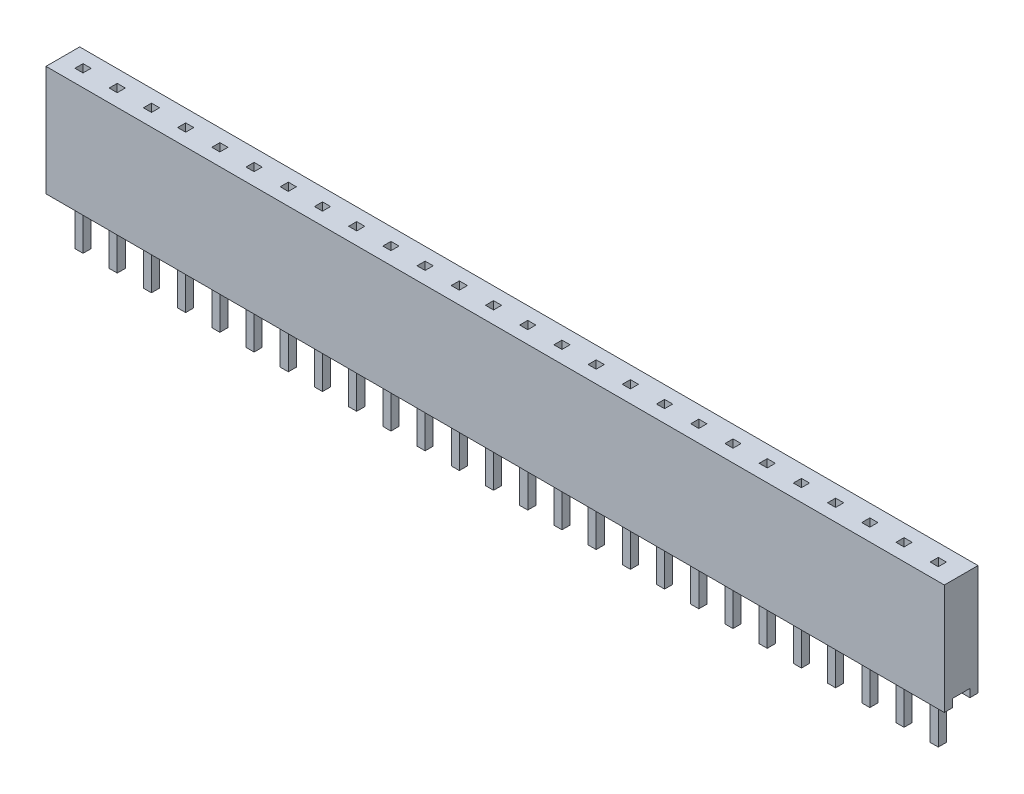
SolidWorks part; units mm, degrees
ref_plane "Front" through (0, 0, 0) normal (0, 0, 1) x (1, 0, 0)
ref_plane "Top" through (0, 0, 0) normal (0, 1, 0) x (1, 0, 0)
ref_plane "Right" through (0, 0, 0) normal (1, 0, 0) x (0, 0, -1)
sketch "Sketch1" plane through (0, 0, 0) normal (0, 1, 0) x (1, 0, 0)
  line L1 (0, 0) -> (66.7004, 0)
  line L2 (0, 0) -> (0, 2.5)
  line L3 (0, 2.5) -> (66.7004, 2.5)
  line L4 (66.7004, 0) -> (66.7004, 2.5)
  dimension "D1" = 66.7004
  dimension "D2" = 2.5
extrude "Body" add sketch "Sketch1" against normal blind 8.2
sketch "Sketch2" plane through (66.7004, 0, 0) normal (1, 0, 0) x (0, 0, -1)
  line L0 (1.25, 0) -> (1.25, -8.2) construction
  line L1 (0, 0) -> (2.5, 0) construction
  line L2 (0, -8.2) -> (2.5, -8.2) construction
  line L3 (0, -8.2) -> (0, 0) construction
  line L4 (0.6, -8.2) -> (1.9, -8.2)
  line L5 (0.6, -8.2) -> (0.6, -7.6)
  line L6 (0.6, -7.6) -> (1.9, -7.6)
  line L7 (1.9, -8.2) -> (1.9, -7.6)
  line L8 (0.6, -8.2) -> (1.9, -7.6) construction
  line L9 (0.6, -7.6) -> (1.9, -8.2) construction
  point P6 (1.25, -7.9)
  dimension "D1" = 0.6
  dimension "D2" = 0.6
extrude "Base Cut" cut sketch "Sketch2" against normal through all
sketch "Sketch3" plane through (0, 0, 0) normal (0, 1, 0) x (1, 0, 0)
  line L0 (0, 1.25) -> (5.2601, 1.25) construction
  line L1 (0, 2.5) -> (0, 0) construction
  line L5 (1.2, 1.55) -> (1.8, 0.95) construction
  line L13 (1.2, 0.95) -> (1.8, 1.55) construction
  line L14 (1.8, 1.55) -> (1.8, 0.95)
  line L15 (1.2, 1.55) -> (1.8, 1.55)
  line L16 (1.2, 1.55) -> (1.2, 0.95)
  line L17 (1.2, 0.95) -> (1.8, 0.95)
  point P11 (1.5, 1.25)
  dimension "D1" = 0.6
  dimension "D2" = 0.6
  dimension "D3" = 1.5
extrude "Pin Hole" cut sketch "Sketch3" against normal through all
pattern_linear "LPattern1" count 26 spacing 2.54 along (1, 0, 0) of "Pin Hole"
sketch "Sketch5" plane through (0, -7.6, 0) normal (0, -1, 0) x (1, 0, 0)
  line L0 (1.8, -0.95) -> (1.8, -1.55) construction
  line L1 (1.8, -1.55) -> (1.2, -1.55) construction
  line L2 (1.2, -1.55) -> (1.2, -0.95) construction
  line L3 (1.2, -0.95) -> (1.8, -0.95) construction
  line L4 (1.8, -0.95) -> (1.8, -1.55)
  line L5 (1.8, -1.55) -> (1.2, -1.55)
  line L6 (1.2, -1.55) -> (1.2, -0.95)
  line L7 (1.2, -0.95) -> (1.8, -0.95)
  line L16 (4.34, -0.95) -> (4.34, -1.55)
  line L17 (4.34, -1.55) -> (3.74, -1.55)
  line L18 (3.74, -1.55) -> (3.74, -0.95)
  line L19 (3.74, -0.95) -> (4.34, -0.95)
  line L24 (6.88, -0.95) -> (6.88, -1.55)
  line L25 (6.88, -1.55) -> (6.28, -1.55)
  line L26 (6.28, -1.55) -> (6.28, -0.95)
  line L27 (6.28, -0.95) -> (6.88, -0.95)
  line L32 (9.42, -0.95) -> (9.42, -1.55)
  line L33 (9.42, -1.55) -> (8.82, -1.55)
  line L34 (8.82, -1.55) -> (8.82, -0.95)
  line L35 (8.82, -0.95) -> (9.42, -0.95)
  line L40 (11.96, -0.95) -> (11.96, -1.55)
  line L41 (11.96, -1.55) -> (11.36, -1.55)
  line L42 (11.36, -1.55) -> (11.36, -0.95)
  line L43 (11.36, -0.95) -> (11.96, -0.95)
  line L48 (14.5, -0.95) -> (14.5, -1.55)
  line L49 (14.5, -1.55) -> (13.9, -1.55)
  line L50 (13.9, -1.55) -> (13.9, -0.95)
  line L51 (13.9, -0.95) -> (14.5, -0.95)
  line L56 (17.04, -0.95) -> (17.04, -1.55)
  line L57 (17.04, -1.55) -> (16.44, -1.55)
  line L58 (16.44, -1.55) -> (16.44, -0.95)
  line L59 (16.44, -0.95) -> (17.04, -0.95)
  line L64 (19.58, -0.95) -> (19.58, -1.55)
  line L65 (19.58, -1.55) -> (18.98, -1.55)
  line L66 (18.98, -1.55) -> (18.98, -0.95)
  line L67 (18.98, -0.95) -> (19.58, -0.95)
  line L72 (22.12, -0.95) -> (22.12, -1.55)
  line L73 (22.12, -1.55) -> (21.52, -1.55)
  line L74 (21.52, -1.55) -> (21.52, -0.95)
  line L75 (21.52, -0.95) -> (22.12, -0.95)
  line L80 (24.66, -0.95) -> (24.66, -1.55)
  line L81 (24.66, -1.55) -> (24.06, -1.55)
  line L82 (24.06, -1.55) -> (24.06, -0.95)
  line L83 (24.06, -0.95) -> (24.66, -0.95)
  line L88 (27.2, -0.95) -> (27.2, -1.55)
  line L89 (27.2, -1.55) -> (26.6, -1.55)
  line L90 (26.6, -1.55) -> (26.6, -0.95)
  line L91 (26.6, -0.95) -> (27.2, -0.95)
  line L96 (29.74, -0.95) -> (29.74, -1.55)
  line L97 (29.74, -1.55) -> (29.14, -1.55)
  line L98 (29.14, -1.55) -> (29.14, -0.95)
  line L99 (29.14, -0.95) -> (29.74, -0.95)
  line L104 (32.28, -0.95) -> (32.28, -1.55)
  line L105 (32.28, -1.55) -> (31.68, -1.55)
  line L106 (31.68, -1.55) -> (31.68, -0.95)
  line L107 (31.68, -0.95) -> (32.28, -0.95)
  line L112 (34.82, -0.95) -> (34.82, -1.55)
  line L113 (34.82, -1.55) -> (34.22, -1.55)
  line L114 (34.22, -1.55) -> (34.22, -0.95)
  line L115 (34.22, -0.95) -> (34.82, -0.95)
  line L120 (37.36, -0.95) -> (37.36, -1.55)
  line L121 (37.36, -1.55) -> (36.76, -1.55)
  line L122 (36.76, -1.55) -> (36.76, -0.95)
  line L123 (36.76, -0.95) -> (37.36, -0.95)
  line L128 (39.9, -0.95) -> (39.9, -1.55)
  line L129 (39.9, -1.55) -> (39.3, -1.55)
  line L130 (39.3, -1.55) -> (39.3, -0.95)
  line L131 (39.3, -0.95) -> (39.9, -0.95)
  line L136 (42.44, -0.95) -> (42.44, -1.55)
  line L137 (42.44, -1.55) -> (41.84, -1.55)
  line L138 (41.84, -1.55) -> (41.84, -0.95)
  line L139 (41.84, -0.95) -> (42.44, -0.95)
  line L144 (44.98, -0.95) -> (44.98, -1.55)
  line L145 (44.98, -1.55) -> (44.38, -1.55)
  line L146 (44.38, -1.55) -> (44.38, -0.95)
  line L147 (44.38, -0.95) -> (44.98, -0.95)
  line L152 (47.52, -0.95) -> (47.52, -1.55)
  line L153 (47.52, -1.55) -> (46.92, -1.55)
  line L154 (46.92, -1.55) -> (46.92, -0.95)
  line L155 (46.92, -0.95) -> (47.52, -0.95)
  line L160 (50.06, -0.95) -> (50.06, -1.55)
  line L161 (50.06, -1.55) -> (49.46, -1.55)
  line L162 (49.46, -1.55) -> (49.46, -0.95)
  line L163 (49.46, -0.95) -> (50.06, -0.95)
  line L168 (52.6, -0.95) -> (52.6, -1.55)
  line L169 (52.6, -1.55) -> (52, -1.55)
  line L170 (52, -1.55) -> (52, -0.95)
  line L171 (52, -0.95) -> (52.6, -0.95)
  line L176 (55.14, -0.95) -> (55.14, -1.55)
  line L177 (55.14, -1.55) -> (54.54, -1.55)
  line L178 (54.54, -1.55) -> (54.54, -0.95)
  line L179 (54.54, -0.95) -> (55.14, -0.95)
  line L184 (57.68, -0.95) -> (57.68, -1.55)
  line L185 (57.68, -1.55) -> (57.08, -1.55)
  line L186 (57.08, -1.55) -> (57.08, -0.95)
  line L187 (57.08, -0.95) -> (57.68, -0.95)
  line L192 (60.22, -0.95) -> (60.22, -1.55)
  line L193 (60.22, -1.55) -> (59.62, -1.55)
  line L194 (59.62, -1.55) -> (59.62, -0.95)
  line L195 (59.62, -0.95) -> (60.22, -0.95)
  line L200 (62.76, -0.95) -> (62.76, -1.55)
  line L201 (62.76, -1.55) -> (62.16, -1.55)
  line L202 (62.16, -1.55) -> (62.16, -0.95)
  line L203 (62.16, -0.95) -> (62.76, -0.95)
  line L208 (65.3, -0.95) -> (65.3, -1.55)
  line L209 (65.3, -1.55) -> (64.7, -1.55)
  line L210 (64.7, -1.55) -> (64.7, -0.95)
  line L211 (64.7, -0.95) -> (65.3, -0.95)
  line L328 (1.8, -0.95) -> (4.34, -0.95) construction
  line L329 (75.46, -0.95) -> (75.46, -1.55) [skipped]
  line L330 (75.46, -1.55) -> (74.86, -1.55) [skipped]
  line L331 (74.86, -1.55) -> (74.86, -0.95) [skipped]
  line L332 (74.86, -0.95) -> (75.46, -0.95) [skipped]
  line L337 (78, -0.95) -> (78, -1.55) [skipped]
  line L338 (78, -1.55) -> (77.4, -1.55) [skipped]
  line L339 (77.4, -1.55) -> (77.4, -0.95) [skipped]
  line L340 (77.4, -0.95) -> (78, -0.95) [skipped]
  line L345 (80.54, -0.95) -> (80.54, -1.55) [skipped]
  line L346 (80.54, -1.55) -> (79.94, -1.55) [skipped]
  line L347 (79.94, -1.55) -> (79.94, -0.95) [skipped]
  line L348 (79.94, -0.95) -> (80.54, -0.95) [skipped]
  line L353 (83.08, -0.95) -> (83.08, -1.55) [skipped]
  line L354 (83.08, -1.55) -> (82.48, -1.55) [skipped]
  line L355 (82.48, -1.55) -> (82.48, -0.95) [skipped]
  line L356 (82.48, -0.95) -> (83.08, -0.95) [skipped]
  line L361 (85.62, -0.95) -> (85.62, -1.55) [skipped]
  line L362 (85.62, -1.55) -> (85.02, -1.55) [skipped]
  line L363 (85.02, -1.55) -> (85.02, -0.95) [skipped]
  line L364 (85.02, -0.95) -> (85.62, -0.95) [skipped]
  line L369 (88.16, -0.95) -> (88.16, -1.55) [skipped]
  line L370 (88.16, -1.55) -> (87.56, -1.55) [skipped]
  line L371 (87.56, -1.55) -> (87.56, -0.95) [skipped]
  line L372 (87.56, -0.95) -> (88.16, -0.95) [skipped]
  line L377 (90.7, -0.95) -> (90.7, -1.55) [skipped]
  line L378 (90.7, -1.55) -> (90.1, -1.55) [skipped]
  line L379 (90.1, -1.55) -> (90.1, -0.95) [skipped]
  line L380 (90.1, -0.95) -> (90.7, -0.95) [skipped]
  line L385 (93.24, -0.95) -> (93.24, -1.55) [skipped]
  line L386 (93.24, -1.55) -> (92.64, -1.55) [skipped]
  line L387 (92.64, -1.55) -> (92.64, -0.95) [skipped]
  line L388 (92.64, -0.95) -> (93.24, -0.95) [skipped]
  line L393 (95.78, -0.95) -> (95.78, -1.55) [skipped]
  line L394 (95.78, -1.55) -> (95.18, -1.55) [skipped]
  line L395 (95.18, -1.55) -> (95.18, -0.95) [skipped]
  line L396 (95.18, -0.95) -> (95.78, -0.95) [skipped]
  line L401 (98.32, -0.95) -> (98.32, -1.55) [skipped]
  line L402 (98.32, -1.55) -> (97.72, -1.55) [skipped]
  line L403 (97.72, -1.55) -> (97.72, -0.95) [skipped]
  line L404 (97.72, -0.95) -> (98.32, -0.95) [skipped]
  line L409 (100.86, -0.95) -> (100.86, -1.55) [skipped]
  line L410 (100.86, -1.55) -> (100.26, -1.55) [skipped]
  line L411 (100.26, -1.55) -> (100.26, -0.95) [skipped]
  line L412 (100.26, -0.95) -> (100.86, -0.95) [skipped]
  line L417 (67.84, -0.95) -> (67.84, -1.55) [skipped]
  line L418 (67.84, -1.55) -> (67.24, -1.55) [skipped]
  line L419 (67.24, -1.55) -> (67.24, -0.95) [skipped]
  line L420 (67.24, -0.95) -> (67.84, -0.95) [skipped]
  line L421 (70.38, -0.95) -> (70.38, -1.55) [skipped]
  line L422 (70.38, -1.55) -> (69.78, -1.55) [skipped]
  line L423 (69.78, -1.55) -> (69.78, -0.95) [skipped]
  line L424 (69.78, -0.95) -> (70.38, -0.95) [skipped]
  line L425 (72.92, -0.95) -> (72.92, -1.55) [skipped]
  line L426 (72.92, -1.55) -> (72.32, -1.55) [skipped]
  line L427 (72.32, -1.55) -> (72.32, -0.95) [skipped]
  line L428 (72.32, -0.95) -> (72.92, -0.95) [skipped]
  dimension "D1" = 2.54
extrude "PCB Straight Pin" add sketch "Sketch5" along normal blind 4
sketch "Sketch7" plane through (0, -8.2, 0) normal (0, -1, 0) x (1, 0, 0)
  line L0 (1.2, -0.95) -> (1.8, -1.55) construction
  circle A0 centre (1.5, -1.25) radius 0.5
  dimension "D1" = 1
